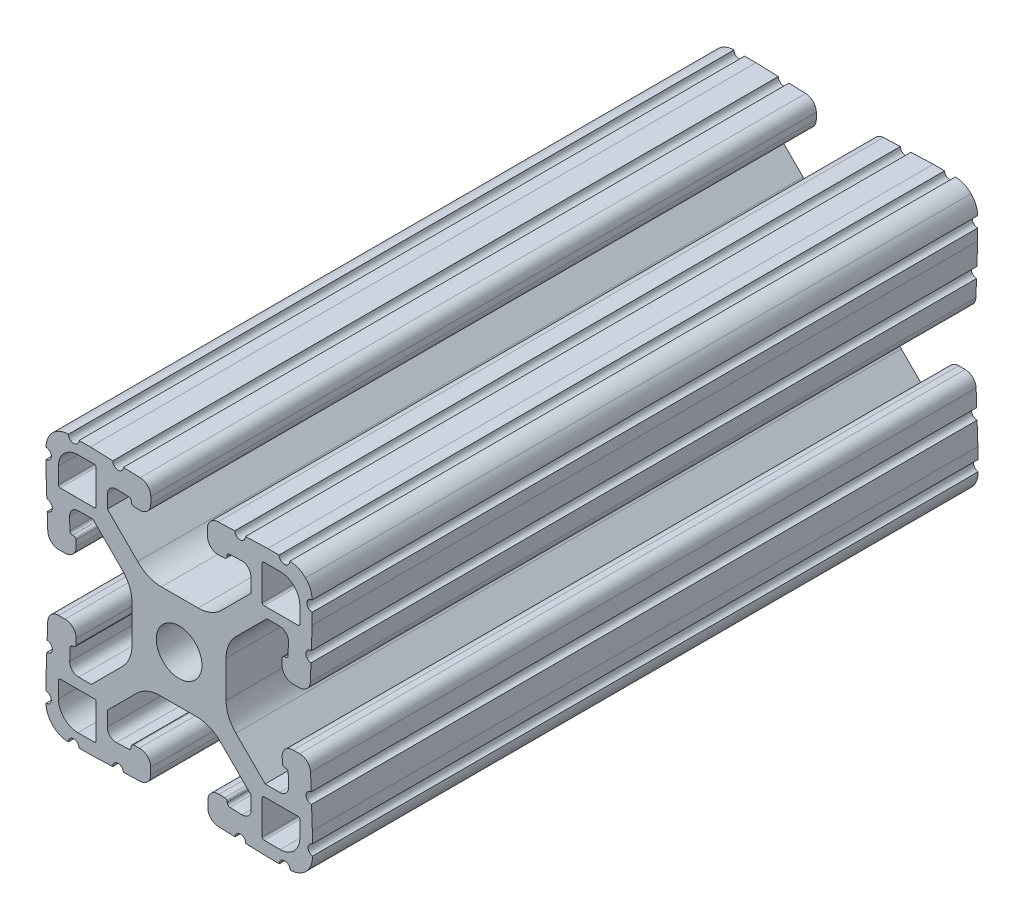
SolidWorks part; units mm, degrees
material "6061-T6 (SS)"
ref_plane "Front Plane" through (0, 0, 0) normal (0, 0, 1) x (1, 0, 0)
ref_plane "Top Plane" through (0, 0, 0) normal (0, 1, 0) x (1, 0, 0)
ref_plane "Right Plane" through (0, 0, 0) normal (1, 0, 0) x (0, 0, -1)
ref_plane "Plane1" through (0, 0, -25.4) normal (0, 0, -1) x (-1, 0, 0)
sketch "Sketch1" plane through (0, 0, -25.4) normal (0, 0, -1) x (-1, 0, 0)
  line L0 (-83.3577, 88.2941) -> (-83.3577, 93.1709)
  line L1 (-83.1037, 93.4249) -> (-80.767, 93.4249)
  line L2 (-77.9729, 90.6309) -> (-77.9729, 88.2941)
  line L3 (-78.2269, 88.0401) -> (-83.1037, 88.0401)
  line L4 (-83.3577, 59.2291) -> (-83.3577, 64.1059)
  line L5 (-83.1037, 64.3599) -> (-78.2269, 64.3599)
  line L6 (-77.9729, 64.1059) -> (-77.9729, 61.7691)
  line L7 (-80.767, 58.9751) -> (-83.1037, 58.9751)
  line L8 (-107.1423, 93.1709) -> (-107.1423, 88.2941)
  line L9 (-107.3963, 88.0401) -> (-112.2731, 88.0401)
  line L10 (-112.5271, 88.2941) -> (-112.5271, 90.6309)
  line L11 (-109.733, 93.4249) -> (-107.3963, 93.4249)
  line L12 (-107.1423, 64.1059) -> (-107.1423, 59.2291)
  line L13 (-107.3963, 58.9751) -> (-109.733, 58.9751)
  line L14 (-112.5271, 61.7691) -> (-112.5271, 64.1059)
  line L15 (-112.2731, 64.3599) -> (-107.3963, 64.3599)
  line L16 (-88.0437, 91.8626) -> (-86.2967, 91.9236)
  line L17 (-84.9824, 90.6544) -> (-84.9824, 88.8002)
  line L18 (-84.9824, 88.8002) -> (-89.3066, 84.476)
  line L19 (-92.7196, 83.0295) -> (-97.9616, 83.0295)
  line L20 (-101.3202, 84.4207) -> (-105.516, 88.6165)
  line L21 (-105.516, 88.6165) -> (-105.516, 90.7313)
  line L22 (-104.2017, 92.0006) -> (-102.4547, 91.9396)
  line L23 (-101.7262, 91.1059) -> (-100.9297, 91.0781)
  line L24 (-99.2999, 92.6519) -> (-99.2999, 93.5668)
  line L25 (-100.8197, 95.1407) -> (-103.2119, 95.2242)
  line L26 (-104.735, 95.2774) -> (-107.9359, 95.3892)
  line L27 (-107.9359, 95.3892) -> (-109.5615, 95.3892)
  line L28 (-114.2859, 90.6648) -> (-114.2859, 89.0392)
  line L29 (-114.2859, 89.0392) -> (-114.1741, 85.8383)
  line L30 (-114.1209, 84.3152) -> (-114.0374, 81.9231)
  line L31 (-112.4635, 80.4032) -> (-111.5486, 80.4032)
  line L32 (-109.9748, 82.033) -> (-110.0026, 82.8295)
  line L33 (-110.8377, 83.5577) -> (-110.8987, 85.3047)
  line L34 (-109.6294, 86.619) -> (-107.8072, 86.619)
  line L35 (-107.8072, 86.619) -> (-103.3649, 82.1768)
  line L36 (-101.9737, 78.8182) -> (-101.9737, 73.576)
  line L37 (-103.3649, 70.2174) -> (-107.5607, 66.0217)
  line L38 (-107.5607, 66.0217) -> (-109.6524, 66.0217)
  line L39 (-110.9217, 67.336) -> (-110.8607, 69.083)
  line L40 (-110.0322, 69.8124) -> (-110.0043, 70.6089)
  line L41 (-111.5782, 72.2387) -> (-112.4931, 72.2387)
  line L42 (-114.0669, 70.7189) -> (-114.1505, 68.3267)
  line L43 (-114.2036, 66.8036) -> (-114.3154, 63.6027)
  line L44 (-114.3154, 63.6027) -> (-114.3154, 61.9626)
  line L45 (-109.6111, 57.1437) -> (-107.9855, 57.1437)
  line L46 (-107.9855, 57.1437) -> (-104.7846, 57.2555)
  line L47 (-103.2615, 57.3086) -> (-100.8694, 57.3922)
  line L48 (-99.3495, 58.966) -> (-99.3495, 59.8809)
  line L49 (-100.9794, 61.4548) -> (-101.7758, 61.4269)
  line L50 (-102.5054, 60.599) -> (-104.2524, 60.538)
  line L51 (-105.5667, 61.8072) -> (-105.5667, 63.6295)
  line L52 (-105.5667, 63.6295) -> (-101.1311, 68.065)
  line L53 (-97.7725, 69.4562) -> (-92.5304, 69.4562)
  line L54 (-89.1717, 68.065) -> (-84.976, 63.8692)
  line L55 (-84.976, 63.8692) -> (-84.976, 61.7811)
  line L56 (-86.2903, 60.5118) -> (-88.0373, 60.5728)
  line L57 (-88.7596, 61.4332) -> (-89.5561, 61.461)
  line L58 (-91.1859, 59.8872) -> (-91.1859, 58.9723)
  line L59 (-89.6661, 57.3985) -> (-87.2739, 57.3149)
  line L60 (-85.7508, 57.2617) -> (-82.5499, 57.15)
  line L61 (-82.5499, 57.15) -> (-80.9244, 57.15)
  line L62 (-76.2, 61.8744) -> (-76.2, 63.4999)
  line L63 (-76.2, 63.4999) -> (-76.3117, 66.7008)
  line L64 (-76.3649, 68.2239) -> (-76.4484, 70.6161)
  line L65 (-78.0223, 72.1359) -> (-78.9372, 72.1359)
  line L66 (-80.511, 70.5061) -> (-80.4832, 69.7096)
  line L67 (-79.6552, 68.9801) -> (-79.5942, 67.2331)
  line L68 (-80.8634, 65.9188) -> (-82.6857, 65.9188)
  line L69 (-82.6857, 65.9188) -> (-87.1213, 70.3543)
  line L70 (-88.5125, 73.7128) -> (-88.5126, 78.955)
  line L71 (-87.1214, 82.3137) -> (-82.9257, 86.5095)
  line L72 (-82.9257, 86.5095) -> (-80.8375, 86.5095)
  line L73 (-79.5682, 85.1951) -> (-79.6293, 83.4482)
  line L74 (-80.4896, 82.7258) -> (-80.5175, 81.9294)
  line L75 (-78.9436, 80.2995) -> (-78.0287, 80.2995)
  line L76 (-76.4549, 81.8194) -> (-76.3713, 84.2115)
  line L77 (-76.3182, 85.7346) -> (-76.2064, 88.9355)
  line L78 (-76.2064, 88.9355) -> (-76.2064, 90.5611)
  line L79 (-80.9308, 95.2855) -> (-82.5564, 95.2855)
  line L80 (-82.5564, 95.2855) -> (-85.7573, 95.1737)
  line L81 (-87.2803, 95.1205) -> (-89.6725, 95.037)
  line L82 (-91.1924, 93.4632) -> (-91.1924, 92.5483)
  line L83 (-89.5625, 90.9744) -> (-88.7661, 91.0023)
  arc A0 (-83.3577, 93.1709) -> (-83.1037, 93.4249) centre (-83.1037, 93.1709) cw
  arc A1 (-80.767, 93.4249) -> (-77.9729, 90.6309) centre (-80.7669, 90.6309) cw
  arc A2 (-77.9729, 88.2941) -> (-78.2269, 88.0401) centre (-78.2269, 88.2941) cw
  arc A3 (-83.1037, 88.0401) -> (-83.3577, 88.2941) centre (-83.1037, 88.2941) cw
  arc A4 (-83.1037, 58.9751) -> (-83.3577, 59.2291) centre (-83.1037, 59.2291) cw
  arc A5 (-83.3577, 64.1059) -> (-83.1037, 64.3599) centre (-83.1037, 64.1059) cw
  arc A6 (-78.2269, 64.3599) -> (-77.9729, 64.1059) centre (-78.2269, 64.1059) cw
  arc A7 (-77.9729, 61.7691) -> (-80.767, 58.9751) centre (-80.7669, 61.7691) cw
  arc A8 (-107.3963, 93.4249) -> (-107.1423, 93.1709) centre (-107.3963, 93.1709) cw
  arc A9 (-107.1423, 88.2941) -> (-107.3963, 88.0401) centre (-107.3963, 88.2941) cw
  arc A10 (-112.2731, 88.0401) -> (-112.5271, 88.2941) centre (-112.2731, 88.2941) cw
  arc A11 (-112.5271, 90.6309) -> (-109.733, 93.4249) centre (-109.7331, 90.6309) cw
  arc A12 (-107.1423, 59.2291) -> (-107.3963, 58.9751) centre (-107.3963, 59.2291) cw
  arc A13 (-109.733, 58.9751) -> (-112.5271, 61.7691) centre (-109.7331, 61.7691) cw
  arc A14 (-112.5271, 64.1059) -> (-112.2731, 64.3599) centre (-112.2731, 64.1059) cw
  arc A15 (-107.3963, 64.3599) -> (-107.1423, 64.1059) centre (-107.3963, 64.1059) cw
  circle A16 centre (-95.25, 76.2) radius 3.2639
  arc A17 (-88.7661, 91.0023) -> (-88.3984, 91.383) centre (-88.7794, 91.383) ccw
  arc A18 (-88.3984, 91.383) -> (-88.0437, 91.8626) centre (-88.0304, 91.4819) cw
  arc A19 (-86.2967, 91.9236) -> (-84.9824, 90.6544) centre (-86.2524, 90.6544) cw
  arc A20 (-89.3066, 84.476) -> (-92.7196, 83.0295) centre (-92.7196, 87.7793) cw
  arc A21 (-97.9616, 83.0295) -> (-101.3202, 84.4207) centre (-97.9616, 87.7793) cw
  arc A22 (-105.516, 90.7313) -> (-104.2017, 92.0006) centre (-104.246, 90.7313) cw
  arc A23 (-102.4547, 91.9396) -> (-102.087, 91.5588) centre (-102.468, 91.5588) cw
  arc A24 (-102.087, 91.5588) -> (-101.7262, 91.1059) centre (-101.7129, 91.4867) ccw
  arc A25 (-100.9297, 91.0781) -> (-99.2999, 92.6519) centre (-100.8747, 92.6519) ccw
  arc A26 (-99.2999, 93.5668) -> (-100.8197, 95.1407) centre (-100.8747, 93.5668) ccw
  arc A27 (-103.2119, 95.2242) -> (-104.735, 95.2774) centre (-103.9735, 95.2508) cw
  arc A28 (-109.5615, 95.3892) -> (-111.0855, 95.3892) centre (-110.3235, 95.3892) cw
  arc A29 (-111.0855, 95.3892) -> (-113.3432, 94.4465) centre (-111.0855, 92.2142) ccw
  arc A30 (-113.3432, 94.4465) -> (-114.2859, 92.1888) centre (-111.1109, 92.1888) ccw
  arc A31 (-114.2859, 92.1888) -> (-114.2859, 90.6648) centre (-114.2859, 91.4268) cw
  arc A32 (-114.1741, 85.8383) -> (-114.1209, 84.3152) centre (-114.1475, 85.0768) cw
  arc A33 (-114.0374, 81.9231) -> (-112.4635, 80.4032) centre (-112.4635, 81.978) ccw
  arc A34 (-111.5486, 80.4032) -> (-109.9748, 82.033) centre (-111.5486, 81.978) ccw
  arc A35 (-110.0026, 82.8295) -> (-110.3834, 83.1972) centre (-110.3834, 82.8162) ccw
  arc A36 (-110.3834, 83.1972) -> (-110.8377, 83.5577) centre (-110.4569, 83.571) cw
  arc A37 (-110.8987, 85.3047) -> (-109.6294, 86.619) centre (-109.6294, 85.349) cw
  arc A38 (-103.3649, 82.1768) -> (-101.9737, 78.8182) centre (-106.7235, 78.8182) cw
  arc A39 (-101.9737, 73.576) -> (-103.3649, 70.2174) centre (-106.7235, 73.576) cw
  arc A40 (-109.6524, 66.0217) -> (-110.9217, 67.336) centre (-109.6524, 67.2917) cw
  arc A41 (-110.8607, 69.083) -> (-110.4799, 69.4507) centre (-110.4799, 69.0697) cw
  arc A42 (-110.4799, 69.4507) -> (-110.0322, 69.8124) centre (-110.413, 69.8257) ccw
  arc A43 (-110.0043, 70.6089) -> (-111.5782, 72.2387) centre (-111.5782, 70.6639) ccw
  arc A44 (-112.4931, 72.2387) -> (-114.0669, 70.7189) centre (-112.4931, 70.6639) ccw
  arc A45 (-114.1505, 68.3267) -> (-114.2036, 66.8036) centre (-114.1771, 67.5652) cw
  arc A46 (-114.3154, 61.9626) -> (-114.3332, 60.4644) centre (-114.4639, 61.2152) cw
  arc A47 (-114.3332, 60.4644) -> (-113.3928, 58.0864) centre (-111.1605, 60.3441) ccw
  arc A48 (-113.3928, 58.0864) -> (-111.1351, 57.1437) centre (-111.1351, 60.3187) ccw
  arc A49 (-111.1351, 57.1437) -> (-109.6111, 57.1437) centre (-110.3731, 57.1437) cw
  arc A50 (-104.7846, 57.2555) -> (-103.2615, 57.3086) centre (-104.0231, 57.2821) cw
  arc A51 (-100.8694, 57.3922) -> (-99.3495, 58.966) centre (-100.9243, 58.966) ccw
  arc A52 (-99.3495, 59.8809) -> (-100.9794, 61.4548) centre (-100.9243, 59.8809) ccw
  arc A53 (-101.7758, 61.4269) -> (-102.1435, 61.0462) centre (-101.7625, 61.0462) ccw
  arc A54 (-102.1435, 61.0462) -> (-102.5054, 60.599) centre (-102.5187, 60.9797) cw
  arc A55 (-104.2524, 60.538) -> (-105.5667, 61.8072) centre (-104.2967, 61.8072) cw
  arc A56 (-101.1311, 68.065) -> (-97.7725, 69.4562) centre (-97.7725, 64.7064) cw
  arc A57 (-92.5304, 69.4562) -> (-89.1717, 68.065) centre (-92.5304, 64.7064) cw
  arc A58 (-84.976, 61.7811) -> (-86.2903, 60.5118) centre (-86.246, 61.7811) cw
  arc A59 (-88.0373, 60.5728) -> (-88.405, 60.9536) centre (-88.024, 60.9536) cw
  arc A60 (-88.405, 60.9536) -> (-88.7596, 61.4332) centre (-88.7729, 61.0524) ccw
  arc A61 (-89.5561, 61.461) -> (-91.1859, 59.8872) centre (-89.6111, 59.8872) ccw
  arc A62 (-91.1859, 58.9723) -> (-89.6661, 57.3985) centre (-89.6111, 58.9723) ccw
  arc A63 (-87.2739, 57.3149) -> (-85.7508, 57.2617) centre (-86.5124, 57.2883) cw
  arc A64 (-80.9244, 57.15) -> (-79.4004, 57.15) centre (-80.1624, 57.15) cw
  arc A65 (-79.4004, 57.15) -> (-77.1426, 58.0927) centre (-79.4004, 60.325) ccw
  arc A66 (-77.1426, 58.0927) -> (-76.2, 60.3504) centre (-79.375, 60.3504) ccw
  arc A67 (-76.2, 60.3504) -> (-76.2, 61.8744) centre (-76.2, 61.1124) cw
  arc A68 (-76.3117, 66.7008) -> (-76.3649, 68.2239) centre (-76.3383, 67.4624) cw
  arc A69 (-76.4484, 70.6161) -> (-78.0223, 72.1359) centre (-78.0223, 70.5611) ccw
  arc A70 (-78.9372, 72.1359) -> (-80.511, 70.5061) centre (-78.9372, 70.5611) ccw
  arc A71 (-80.4832, 69.7096) -> (-80.1024, 69.342) centre (-80.1024, 69.723) ccw
  arc A72 (-80.1024, 69.342) -> (-79.6552, 68.9801) centre (-80.036, 68.9668) cw
  arc A73 (-79.5942, 67.2331) -> (-80.8634, 65.9188) centre (-80.8634, 67.1888) cw
  arc A74 (-87.1213, 70.3543) -> (-88.5125, 73.7128) centre (-83.7627, 73.7129) cw
  arc A75 (-88.5126, 78.955) -> (-87.1214, 82.3137) centre (-83.7628, 78.9551) cw
  arc A76 (-80.8375, 86.5095) -> (-79.5682, 85.1951) centre (-80.8375, 85.2395) cw
  arc A77 (-79.6293, 83.4482) -> (-80.01, 83.0805) centre (-80.01, 83.4615) cw
  arc A78 (-80.01, 83.0805) -> (-80.4896, 82.7258) centre (-80.1089, 82.7125) ccw
  arc A79 (-80.5175, 81.9294) -> (-78.9436, 80.2995) centre (-78.9436, 81.8743) ccw
  arc A80 (-78.0287, 80.2995) -> (-76.4549, 81.8194) centre (-78.0287, 81.8743) ccw
  arc A81 (-76.3713, 84.2115) -> (-76.3182, 85.7346) centre (-76.3448, 84.9731) cw
  arc A82 (-76.2064, 90.5611) -> (-76.2064, 92.0851) centre (-76.2064, 91.3231) cw
  arc A83 (-76.2064, 92.0851) -> (-77.1491, 94.3428) centre (-79.3814, 92.0851) ccw
  arc A84 (-77.1491, 94.3428) -> (-79.4068, 95.2855) centre (-79.4068, 92.1105) ccw
  arc A85 (-79.4068, 95.2855) -> (-80.9308, 95.2855) centre (-80.1688, 95.2855) cw
  arc A86 (-85.7573, 95.1737) -> (-87.2803, 95.1205) centre (-86.5188, 95.1471) cw
  arc A87 (-89.6725, 95.037) -> (-91.1924, 93.4632) centre (-89.6176, 93.4632) ccw
  arc A88 (-91.1924, 92.5483) -> (-89.5625, 90.9744) centre (-89.6176, 92.5483) ccw
extrude "Boss-Extrude1" add sketch "Sketch1" against normal blind 95.25
